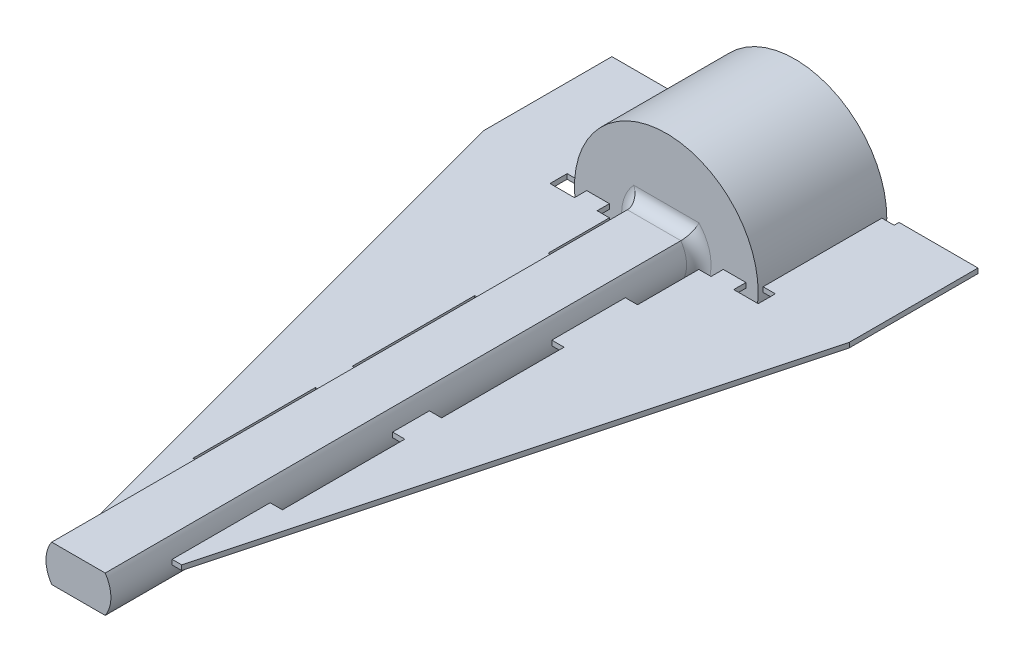
SolidWorks part; units mm, degrees
material "Polylactic Acid (PLA)"
ref_plane "Front Plane" through (0, 0, 0) normal (0, 0, 1) x (1, 0, 0)
ref_plane "Top Plane" through (0, 0, 0) normal (0, 1, 0) x (1, 0, 0)
ref_plane "Right Plane" through (0, 0, 0) normal (1, 0, 0) x (0, 0, -1)
sketch "Sketch2" plane through (0, 0, 0) normal (0, 0, 1) x (1, 0, 0)
  arc A0 (-180.9646, 16.9181) -> (-181.2813, 16.5945) centre (-180.7258, 16.3677) ccw
  arc A1 (-181.2813, 16.5945) -> (-181.4587, 15.6283) centre (-179.0594, 15.6871) ccw
  arc A2 (-181.4587, 15.6283) -> (-180.9368, 15.2683) centre (-178.5779, 19.2465) ccw
  arc A3 (-180.9368, 15.2683) -> (-180.0966, 15.7774) centre (-181.7341, 17.532) ccw
  arc A4 (-180.0966, 15.7774) -> (-179.9066, 16.1884) centre (-180.506, 16.216) ccw
  arc A5 (-179.7695, 16.2766) -> (-179.9066, 16.1884) centre (-179.8067, 16.1838) ccw
  arc A6 (-179.7695, 16.2766) -> (-179.5312, 16.1918) centre (-178.5779, 19.2465) ccw
  arc A7 (-179.4806, 16.0368) -> (-179.5312, 16.1918) centre (-179.561, 16.0963) ccw
  arc A8 (-179.4806, 16.0368) -> (-179.5931, 15.5981) centre (-178.9987, 15.6794) ccw
  arc A9 (-179.5931, 15.5981) -> (-179.2637, 14.6726) centre (-177.2152, 15.9232) ccw
  arc A10 (-179.2637, 14.6726) -> (-178.6317, 14.6218) centre (-178.5779, 19.2465) ccw
  arc A11 (-178.6317, 14.6218) -> (-178.1586, 15.4828) centre (-180.454, 16.1836) ccw
  arc A12 (-178.1586, 15.4828) -> (-178.1996, 15.9338) centre (-178.7324, 15.658) ccw
  arc A13 (-178.1249, 16.0787) -> (-178.1996, 15.9338) centre (-178.1108, 15.9797) ccw
  arc A14 (-178.1249, 16.0787) -> (-177.8761, 16.1244) centre (-178.5779, 19.2465) ccw
  arc A15 (-177.7548, 16.0154) -> (-177.8761, 16.1244) centre (-177.8542, 16.0268) ccw
  arc A16 (-177.7548, 16.0154) -> (-177.6329, 15.5793) centre (-177.1587, 15.9469) ccw
  arc A17 (-177.6329, 15.5793) -> (-176.8848, 14.9425) centre (-175.7362, 17.0498) ccw
  arc A18 (-176.8848, 14.9425) -> (-176.3121, 15.2145) centre (-178.5779, 19.2465) ccw
  arc A19 (-176.3121, 15.2145) -> (-176.3329, 16.1967) centre (-178.6712, 15.6559) ccw
  arc A20 (-176.3329, 16.1967) -> (-176.5939, 16.5668) centre (-176.9175, 16.0615) ccw
  arc A21 (-176.6017, 16.7296) -> (-176.5939, 16.5668) centre (-176.54, 16.651) ccw
  arc A22 (-176.6017, 16.7296) -> (-176.4091, 16.8936) centre (-178.5779, 19.2465) ccw
  arc A23 (-176.2496, 16.8599) -> (-176.4091, 16.8936) centre (-176.3413, 16.8201) ccw
  arc A24 (-176.2496, 16.8599) -> (-175.926, 16.5431) centre (-175.6991, 17.0986) ccw
  arc A25 (-175.926, 16.5431) -> (-174.9597, 16.3657) centre (-175.0185, 18.765) ccw
  arc A26 (-174.9597, 16.3657) -> (-174.5997, 16.8876) centre (-178.5779, 19.2465) ccw
  arc A27 (-174.5997, 16.8876) -> (-175.1088, 17.7278) centre (-176.8634, 16.0903) ccw
  arc A28 (-175.1088, 17.7278) -> (-175.5198, 17.9178) centre (-175.5475, 17.3184) ccw
  arc A29 (-175.608, 18.0549) -> (-175.5198, 17.9178) centre (-175.5152, 18.0177) ccw
  arc A30 (-175.608, 18.0549) -> (-175.5232, 18.2932) centre (-178.5779, 19.2465) ccw
  arc A31 (-175.3682, 18.3438) -> (-175.5232, 18.2932) centre (-175.4277, 18.2635) ccw
  arc A32 (-175.3682, 18.3438) -> (-174.9296, 18.2313) centre (-175.0108, 18.8258) ccw
  arc A33 (-174.9296, 18.2313) -> (-174.004, 18.5608) centre (-175.2546, 20.6092) ccw
  arc A34 (-174.004, 18.5608) -> (-173.9532, 19.1927) centre (-178.5779, 19.2465) ccw
  arc A35 (-173.9532, 19.1927) -> (-174.8142, 19.6658) centre (-175.515, 17.3704) ccw
  arc A36 (-174.8142, 19.6658) -> (-175.2652, 19.6248) centre (-174.9894, 19.092) ccw
  arc A37 (-175.4102, 19.6995) -> (-175.2652, 19.6248) centre (-175.3112, 19.7137) ccw
  arc A38 (-175.4102, 19.6995) -> (-175.4558, 19.9483) centre (-178.5779, 19.2465) ccw
  arc A39 (-175.3469, 20.0696) -> (-175.4558, 19.9483) centre (-175.3583, 19.9702) ccw
  arc A40 (-175.3469, 20.0696) -> (-174.9108, 20.1915) centre (-175.2784, 20.6657) ccw
  arc A41 (-174.9108, 20.1915) -> (-174.274, 20.9396) centre (-176.3812, 22.0882) ccw
  arc A42 (-174.274, 20.9396) -> (-174.5459, 21.5123) centre (-178.5779, 19.2465) ccw
  arc A43 (-174.5459, 21.5123) -> (-175.5282, 21.4915) centre (-174.9873, 19.1532) ccw
  arc A44 (-175.5282, 21.4915) -> (-175.8982, 21.2305) centre (-175.3929, 20.9069) ccw
  arc A45 (-176.0611, 21.2227) -> (-175.8982, 21.2305) centre (-175.9824, 21.2845) ccw
  arc A46 (-176.0611, 21.2227) -> (-176.225, 21.4153) centre (-178.5779, 19.2465) ccw
  arc A47 (-176.1913, 21.5749) -> (-176.225, 21.4153) centre (-176.1515, 21.4831) ccw
  arc A48 (-176.1913, 21.5749) -> (-175.8746, 21.8985) centre (-176.43, 22.1253) ccw
  arc A49 (-175.8746, 21.8985) -> (-175.6971, 22.8647) centre (-178.0964, 22.8059) ccw
  arc A50 (-175.6971, 22.8647) -> (-176.219, 23.2247) centre (-178.5779, 19.2465) ccw
  arc A51 (-176.219, 23.2247) -> (-177.0592, 22.7156) centre (-175.4217, 20.961) ccw
  arc A52 (-177.0592, 22.7156) -> (-177.2492, 22.3046) centre (-176.6499, 22.277) ccw
  arc A53 (-177.3864, 22.2164) -> (-177.2492, 22.3046) centre (-177.3491, 22.3092) ccw
  arc A54 (-177.3864, 22.2164) -> (-177.6247, 22.3012) centre (-178.5779, 19.2465) ccw
  arc A55 (-177.6752, 22.4562) -> (-177.6247, 22.3012) centre (-177.5949, 22.3967) ccw
  arc A56 (-177.6752, 22.4562) -> (-177.5627, 22.8948) centre (-178.1572, 22.8136) ccw
  arc A57 (-177.5627, 22.8948) -> (-177.8922, 23.8204) centre (-179.9406, 22.5698) ccw
  arc A58 (-177.8922, 23.8204) -> (-178.5242, 23.8712) centre (-178.5779, 19.2465) ccw
  arc A59 (-178.5242, 23.8712) -> (-178.9973, 23.0102) centre (-176.7018, 22.3094) ccw
  arc A60 (-178.9973, 23.0102) -> (-178.9563, 22.5592) centre (-178.4234, 22.835) ccw
  arc A61 (-179.0309, 22.4143) -> (-178.9563, 22.5592) centre (-179.0451, 22.5133) ccw
  arc A62 (-179.0309, 22.4143) -> (-179.2797, 22.3686) centre (-178.5779, 19.2465) ccw
  arc A63 (-179.401, 22.4776) -> (-179.2797, 22.3686) centre (-179.3017, 22.4661) ccw
  arc A64 (-179.401, 22.4776) -> (-179.5229, 22.9137) centre (-179.9971, 22.546) ccw
  arc A65 (-179.5229, 22.9137) -> (-180.271, 23.5505) centre (-181.4197, 21.4432) ccw
  arc A66 (-180.271, 23.5505) -> (-180.8437, 23.2785) centre (-178.5779, 19.2465) ccw
  arc A67 (-180.8437, 23.2785) -> (-180.8229, 22.2963) centre (-178.4846, 22.8371) ccw
  arc A68 (-180.8229, 22.2963) -> (-180.562, 21.9262) centre (-180.2383, 22.4315) ccw
  arc A69 (-180.5541, 21.7634) -> (-180.562, 21.9262) centre (-180.6159, 21.842) ccw
  arc A70 (-180.5541, 21.7634) -> (-180.7468, 21.5994) centre (-178.5779, 19.2465) ccw
  arc A71 (-180.9063, 21.6331) -> (-180.7468, 21.5994) centre (-180.8145, 21.6729) ccw
  arc A72 (-180.9063, 21.6331) -> (-181.2299, 21.9499) centre (-181.4567, 21.3944) ccw
  arc A73 (-181.2299, 21.9499) -> (-182.1962, 22.1273) centre (-182.1373, 19.728) ccw
  arc A74 (-182.1962, 22.1273) -> (-182.5561, 21.6054) centre (-178.5779, 19.2465) ccw
  arc A75 (-182.5561, 21.6054) -> (-182.047, 20.7652) centre (-180.2924, 22.4027) ccw
  arc A76 (-182.047, 20.7652) -> (-181.636, 20.5752) centre (-181.6084, 21.1746) ccw
  arc A77 (-181.5478, 20.4381) -> (-181.636, 20.5752) centre (-181.6406, 20.4753) ccw
  arc A78 (-181.5478, 20.4381) -> (-181.6326, 20.1997) centre (-178.5779, 19.2465) ccw
  arc A79 (-181.7877, 20.1492) -> (-181.6326, 20.1997) centre (-181.7281, 20.2295) ccw
  arc A80 (-181.7877, 20.1492) -> (-182.2263, 20.2617) centre (-182.145, 19.6672) ccw
  arc A81 (-182.2263, 20.2617) -> (-183.1518, 19.9322) centre (-181.9012, 17.8838) ccw
  arc A82 (-183.1518, 19.9322) -> (-183.2026, 19.3002) centre (-178.5779, 19.2465) ccw
  arc A83 (-183.2026, 19.3002) -> (-182.3416, 18.8272) centre (-181.6408, 21.1226) ccw
  arc A84 (-182.3416, 18.8272) -> (-181.8906, 18.8681) centre (-182.1664, 19.401) ccw
  arc A85 (-181.7457, 18.7935) -> (-181.8906, 18.8681) centre (-181.8447, 18.7793) ccw
  arc A86 (-181.7457, 18.7935) -> (-181.7, 18.5447) centre (-178.5779, 19.2465) ccw
  arc A87 (-181.809, 18.4234) -> (-181.7, 18.5447) centre (-181.7976, 18.5227) ccw
  arc A88 (-181.809, 18.4234) -> (-182.2451, 18.3015) centre (-181.8775, 17.8273) ccw
  arc A89 (-182.2451, 18.3015) -> (-182.8819, 17.5534) centre (-180.7746, 16.4047) ccw
  arc A90 (-182.8819, 17.5534) -> (-182.6099, 16.9807) centre (-178.5779, 19.2465) ccw
  arc A91 (-182.6099, 16.9807) -> (-181.6277, 17.0015) centre (-182.1685, 19.3398) ccw
  arc A92 (-181.6277, 17.0015) -> (-181.2576, 17.2625) centre (-181.7629, 17.5861) ccw
  arc A93 (-181.0948, 17.2703) -> (-181.2576, 17.2625) centre (-181.1734, 17.2085) ccw
  arc A94 (-181.0948, 17.2703) -> (-180.9308, 17.0777) centre (-178.5779, 19.2465) ccw
  arc A95 (-180.9646, 16.9181) -> (-180.9308, 17.0777) centre (-181.0043, 17.0099) ccw
  arc A96 (-180.9248, 16.8264) -> (-181.1887, 16.5567) centre (-180.7258, 16.3677) ccw
  arc A97 (-181.1887, 16.5567) -> (-181.3594, 15.6773) centre (-179.0594, 15.6871) ccw
  arc A98 (-181.3594, 15.6773) -> (-180.9262, 15.3785) centre (-178.5779, 19.2465) ccw
  arc A99 (-180.9262, 15.3785) -> (-180.1648, 15.8505) centre (-181.7341, 17.532) ccw
  arc A100 (-180.1648, 15.8505) -> (-180.0065, 16.193) centre (-180.506, 16.216) ccw
  arc A101 (-179.7323, 16.3694) -> (-180.0065, 16.193) centre (-179.8067, 16.1838) ccw
  arc A102 (-179.7323, 16.3694) -> (-179.5014, 16.2872) centre (-178.5779, 19.2465) ccw
  arc A103 (-179.4003, 15.9772) -> (-179.5014, 16.2872) centre (-179.561, 16.0963) ccw
  arc A104 (-179.4003, 15.9772) -> (-179.494, 15.6117) centre (-178.9987, 15.6794) ccw
  arc A105 (-179.494, 15.6117) -> (-179.2022, 14.7648) centre (-177.2152, 15.9232) ccw
  arc A106 (-179.2022, 14.7648) -> (-178.6776, 14.7226) centre (-178.5779, 19.2465) ccw
  arc A107 (-178.6776, 14.7226) -> (-178.2542, 15.512) centre (-180.454, 16.1836) ccw
  arc A108 (-178.2542, 15.512) -> (-178.2884, 15.8878) centre (-178.7324, 15.658) ccw
  arc A109 (-178.1391, 16.1777) -> (-178.2884, 15.8878) centre (-178.1108, 15.9797) ccw
  arc A110 (-178.1391, 16.1777) -> (-177.898, 16.222) centre (-178.5779, 19.2465) ccw
  arc A111 (-177.6555, 16.004) -> (-177.898, 16.222) centre (-177.8542, 16.0268) ccw
  arc A112 (-177.6555, 16.004) -> (-177.5539, 15.6406) centre (-177.1587, 15.9469) ccw
  arc A113 (-177.5539, 15.6406) -> (-176.8777, 15.0531) centre (-175.7362, 17.0498) ccw
  arc A114 (-176.8777, 15.0531) -> (-176.4023, 15.2788) centre (-178.5779, 19.2465) ccw
  arc A115 (-176.4023, 15.2788) -> (-176.4304, 16.1742) centre (-178.6712, 15.6559) ccw
  arc A116 (-176.4304, 16.1742) -> (-176.6478, 16.4826) centre (-176.9175, 16.0615) ccw
  arc A117 (-176.6635, 16.8083) -> (-176.6478, 16.4826) centre (-176.54, 16.651) ccw
  arc A118 (-176.6635, 16.8083) -> (-176.4769, 16.9671) centre (-178.5779, 19.2465) ccw
  arc A119 (-176.1578, 16.8996) -> (-176.4769, 16.9671) centre (-176.3413, 16.8201) ccw
  arc A120 (-176.1578, 16.8996) -> (-175.8881, 16.6357) centre (-175.6991, 17.0986) ccw
  arc A121 (-175.8881, 16.6357) -> (-175.0088, 16.465) centre (-175.0185, 18.765) ccw
  arc A122 (-175.0088, 16.465) -> (-174.71, 16.8982) centre (-178.5779, 19.2465) ccw
  arc A123 (-174.71, 16.8982) -> (-175.1819, 17.6596) centre (-176.8634, 16.0903) ccw
  arc A124 (-175.1819, 17.6596) -> (-175.5244, 17.8179) centre (-175.5475, 17.3184) ccw
  arc A125 (-175.7009, 18.0922) -> (-175.5244, 17.8179) centre (-175.5152, 18.0177) ccw
  arc A126 (-175.7009, 18.0922) -> (-175.6187, 18.323) centre (-178.5779, 19.2465) ccw
  arc A127 (-175.3086, 18.4241) -> (-175.6187, 18.323) centre (-175.4277, 18.2635) ccw
  arc A128 (-175.3086, 18.4241) -> (-174.9431, 18.3304) centre (-175.0108, 18.8258) ccw
  arc A129 (-174.9431, 18.3304) -> (-174.0962, 18.6222) centre (-175.2546, 20.6092) ccw
  arc A130 (-174.0962, 18.6222) -> (-174.054, 19.1468) centre (-178.5779, 19.2465) ccw
  arc A131 (-174.054, 19.1468) -> (-174.8434, 19.5702) centre (-175.515, 17.3704) ccw
  arc A132 (-174.8434, 19.5702) -> (-175.2192, 19.536) centre (-174.9894, 19.092) ccw
  arc A133 (-175.5091, 19.6853) -> (-175.2192, 19.536) centre (-175.3112, 19.7137) ccw
  arc A134 (-175.5091, 19.6853) -> (-175.5534, 19.9264) centre (-178.5779, 19.2465) ccw
  arc A135 (-175.3354, 20.1689) -> (-175.5534, 19.9264) centre (-175.3583, 19.9702) ccw
  arc A136 (-175.3354, 20.1689) -> (-174.972, 20.2705) centre (-175.2784, 20.6657) ccw
  arc A137 (-174.972, 20.2705) -> (-174.3845, 20.9467) centre (-176.3812, 22.0882) ccw
  arc A138 (-174.3845, 20.9467) -> (-174.6103, 21.4221) centre (-178.5779, 19.2465) ccw
  arc A139 (-174.6103, 21.4221) -> (-175.5056, 21.3941) centre (-174.9873, 19.1532) ccw
  arc A140 (-175.5056, 21.3941) -> (-175.814, 21.1766) centre (-175.3929, 20.9069) ccw
  arc A141 (-176.1397, 21.1609) -> (-175.814, 21.1766) centre (-175.9824, 21.2845) ccw
  arc A142 (-176.1397, 21.1609) -> (-176.2986, 21.3476) centre (-178.5779, 19.2465) ccw
  arc A143 (-176.2311, 21.6666) -> (-176.2986, 21.3476) centre (-176.1515, 21.4831) ccw
  arc A144 (-176.2311, 21.6666) -> (-175.9671, 21.9363) centre (-176.43, 22.1253) ccw
  arc A145 (-175.9671, 21.9363) -> (-175.7964, 22.8156) centre (-178.0964, 22.8059) ccw
  arc A146 (-175.7964, 22.8156) -> (-176.2296, 23.1145) centre (-178.5779, 19.2465) ccw
  arc A147 (-176.2296, 23.1145) -> (-176.991, 22.6425) centre (-175.4217, 20.961) ccw
  arc A148 (-176.991, 22.6425) -> (-177.1493, 22.3) centre (-176.6499, 22.277) ccw
  arc A149 (-177.4236, 22.1236) -> (-177.1493, 22.3) centre (-177.3491, 22.3092) ccw
  arc A150 (-177.4236, 22.1236) -> (-177.6545, 22.2058) centre (-178.5779, 19.2465) ccw
  arc A151 (-177.7555, 22.5158) -> (-177.6545, 22.2058) centre (-177.5949, 22.3967) ccw
  arc A152 (-177.7555, 22.5158) -> (-177.6618, 22.8813) centre (-178.1572, 22.8136) ccw
  arc A153 (-177.6618, 22.8813) -> (-177.9536, 23.7282) centre (-179.9406, 22.5698) ccw
  arc A154 (-177.9536, 23.7282) -> (-178.4782, 23.7704) centre (-178.5779, 19.2465) ccw
  arc A155 (-178.4782, 23.7704) -> (-178.9016, 22.981) centre (-176.7018, 22.3094) ccw
  arc A156 (-178.9016, 22.981) -> (-178.8675, 22.6052) centre (-178.4234, 22.835) ccw
  arc A157 (-179.0168, 22.3153) -> (-178.8675, 22.6052) centre (-179.0451, 22.5133) ccw
  arc A158 (-179.0168, 22.3153) -> (-179.2578, 22.271) centre (-178.5779, 19.2465) ccw
  arc A159 (-179.5004, 22.489) -> (-179.2578, 22.271) centre (-179.3017, 22.4661) ccw
  arc A160 (-179.5004, 22.489) -> (-179.6019, 22.8524) centre (-179.9971, 22.546) ccw
  arc A161 (-179.6019, 22.8524) -> (-180.2781, 23.4399) centre (-181.4197, 21.4432) ccw
  arc A162 (-180.2781, 23.4399) -> (-180.7535, 23.2142) centre (-178.5779, 19.2465) ccw
  arc A163 (-180.7535, 23.2142) -> (-180.7255, 22.3188) centre (-178.4846, 22.8371) ccw
  arc A164 (-180.7255, 22.3188) -> (-180.508, 22.0104) centre (-180.2383, 22.4315) ccw
  arc A165 (-180.4924, 21.6847) -> (-180.508, 22.0104) centre (-180.6159, 21.842) ccw
  arc A166 (-180.4924, 21.6847) -> (-180.679, 21.5259) centre (-178.5779, 19.2465) ccw
  arc A167 (-180.998, 21.5933) -> (-180.679, 21.5259) centre (-180.8145, 21.6729) ccw
  arc A168 (-180.998, 21.5933) -> (-181.2677, 21.8573) centre (-181.4567, 21.3944) ccw
  arc A169 (-181.2677, 21.8573) -> (-182.1471, 22.028) centre (-182.1373, 19.728) ccw
  arc A170 (-182.1471, 22.028) -> (-182.4459, 21.5948) centre (-178.5779, 19.2465) ccw
  arc A171 (-182.4459, 21.5948) -> (-181.9739, 20.8334) centre (-180.2924, 22.4027) ccw
  arc A172 (-181.9739, 20.8334) -> (-181.6314, 20.6751) centre (-181.6084, 21.1746) ccw
  arc A173 (-181.455, 20.4008) -> (-181.6314, 20.6751) centre (-181.6406, 20.4753) ccw
  arc A174 (-181.455, 20.4008) -> (-181.5372, 20.17) centre (-178.5779, 19.2465) ccw
  arc A175 (-181.8472, 20.0689) -> (-181.5372, 20.17) centre (-181.7281, 20.2295) ccw
  arc A176 (-181.8472, 20.0689) -> (-182.2127, 20.1626) centre (-182.145, 19.6672) ccw
  arc A177 (-182.2127, 20.1626) -> (-183.0597, 19.8708) centre (-181.9012, 17.8838) ccw
  arc A178 (-183.0597, 19.8708) -> (-183.1018, 19.3462) centre (-178.5779, 19.2465) ccw
  arc A179 (-183.1018, 19.3462) -> (-182.3124, 18.9228) centre (-181.6408, 21.1226) ccw
  arc A180 (-182.3124, 18.9228) -> (-181.9366, 18.9569) centre (-182.1664, 19.401) ccw
  arc A181 (-181.6467, 18.8076) -> (-181.9366, 18.9569) centre (-181.8447, 18.7793) ccw
  arc A182 (-181.6467, 18.8076) -> (-181.6024, 18.5666) centre (-178.5779, 19.2465) ccw
  arc A183 (-181.8204, 18.324) -> (-181.6024, 18.5666) centre (-181.7976, 18.5227) ccw
  arc A184 (-181.8204, 18.324) -> (-182.1838, 18.2225) centre (-181.8775, 17.8273) ccw
  arc A185 (-182.1838, 18.2225) -> (-182.7714, 17.5463) centre (-180.7746, 16.4047) ccw
  arc A186 (-182.7714, 17.5463) -> (-182.5456, 17.0709) centre (-178.5779, 19.2465) ccw
  arc A187 (-182.5456, 17.0709) -> (-181.6502, 17.0989) centre (-182.1685, 19.3398) ccw
  arc A188 (-181.6502, 17.0989) -> (-181.3419, 17.3164) centre (-181.7629, 17.5861) ccw
  arc A189 (-181.0161, 17.332) -> (-181.3419, 17.3164) centre (-181.1734, 17.2085) ccw
  arc A190 (-181.0161, 17.332) -> (-180.8573, 17.1454) centre (-178.5779, 19.2465) ccw
  arc A191 (-180.9248, 16.8264) -> (-180.8573, 17.1454) centre (-181.0043, 17.0099) ccw
  arc A192 (-180.9248, 16.8264) -> (-181.1887, 16.5567) centre (-180.7258, 16.3677) ccw construction
  arc A193 (-181.1887, 16.5567) -> (-181.3594, 15.6773) centre (-179.0594, 15.6871) ccw construction
  arc A194 (-181.3594, 15.6773) -> (-180.9262, 15.3785) centre (-178.5779, 19.2465) ccw construction
  arc A195 (-180.9262, 15.3785) -> (-180.1648, 15.8505) centre (-181.7341, 17.532) ccw construction
  arc A196 (-180.1648, 15.8505) -> (-180.0065, 16.193) centre (-180.506, 16.216) ccw construction
  arc A197 (-179.7323, 16.3694) -> (-180.0065, 16.193) centre (-179.8067, 16.1838) ccw construction
  arc A198 (-179.7323, 16.3694) -> (-179.5014, 16.2872) centre (-178.5779, 19.2465) ccw construction
  arc A199 (-179.4003, 15.9772) -> (-179.5014, 16.2872) centre (-179.561, 16.0963) ccw construction
  arc A200 (-179.4003, 15.9772) -> (-179.494, 15.6117) centre (-178.9987, 15.6794) ccw construction
  arc A201 (-179.494, 15.6117) -> (-179.2022, 14.7648) centre (-177.2152, 15.9232) ccw construction
  arc A202 (-179.2022, 14.7648) -> (-178.6776, 14.7226) centre (-178.5779, 19.2465) ccw construction
  arc A203 (-178.6776, 14.7226) -> (-178.2542, 15.512) centre (-180.454, 16.1836) ccw construction
  arc A204 (-178.2542, 15.512) -> (-178.2884, 15.8878) centre (-178.7324, 15.658) ccw construction
  arc A205 (-178.1391, 16.1777) -> (-178.2884, 15.8878) centre (-178.1108, 15.9797) ccw construction
  arc A206 (-178.1391, 16.1777) -> (-177.898, 16.222) centre (-178.5779, 19.2465) ccw construction
  arc A207 (-177.6555, 16.004) -> (-177.898, 16.222) centre (-177.8542, 16.0268) ccw construction
  arc A208 (-177.6555, 16.004) -> (-177.5539, 15.6406) centre (-177.1587, 15.9469) ccw construction
  arc A209 (-177.5539, 15.6406) -> (-176.8777, 15.0531) centre (-175.7362, 17.0498) ccw construction
  arc A210 (-176.8777, 15.0531) -> (-176.4023, 15.2788) centre (-178.5779, 19.2465) ccw construction
  arc A211 (-176.4023, 15.2788) -> (-176.4304, 16.1742) centre (-178.6712, 15.6559) ccw construction
  arc A212 (-176.4304, 16.1742) -> (-176.6478, 16.4826) centre (-176.9175, 16.0615) ccw construction
  arc A213 (-176.6635, 16.8083) -> (-176.6478, 16.4826) centre (-176.54, 16.651) ccw construction
  arc A214 (-176.6635, 16.8083) -> (-176.4769, 16.9671) centre (-178.5779, 19.2465) ccw construction
  arc A215 (-176.1578, 16.8996) -> (-176.4769, 16.9671) centre (-176.3413, 16.8201) ccw construction
  arc A216 (-176.1578, 16.8996) -> (-175.8881, 16.6357) centre (-175.6991, 17.0986) ccw construction
  arc A217 (-175.8881, 16.6357) -> (-175.0088, 16.465) centre (-175.0185, 18.765) ccw construction
  arc A218 (-175.0088, 16.465) -> (-174.71, 16.8982) centre (-178.5779, 19.2465) ccw construction
  arc A219 (-174.71, 16.8982) -> (-175.1819, 17.6596) centre (-176.8634, 16.0903) ccw construction
  arc A220 (-175.1819, 17.6596) -> (-175.5244, 17.8179) centre (-175.5475, 17.3184) ccw construction
  arc A221 (-175.7009, 18.0922) -> (-175.5244, 17.8179) centre (-175.5152, 18.0177) ccw construction
  arc A222 (-175.7009, 18.0922) -> (-175.6187, 18.323) centre (-178.5779, 19.2465) ccw construction
  arc A223 (-175.3086, 18.4241) -> (-175.6187, 18.323) centre (-175.4277, 18.2635) ccw construction
  arc A224 (-175.3086, 18.4241) -> (-174.9431, 18.3304) centre (-175.0108, 18.8258) ccw construction
  arc A225 (-174.9431, 18.3304) -> (-174.0962, 18.6222) centre (-175.2546, 20.6092) ccw construction
  arc A226 (-174.0962, 18.6222) -> (-174.054, 19.1468) centre (-178.5779, 19.2465) ccw construction
  arc A227 (-174.054, 19.1468) -> (-174.8434, 19.5702) centre (-175.515, 17.3704) ccw construction
  arc A228 (-174.8434, 19.5702) -> (-175.2192, 19.536) centre (-174.9894, 19.092) ccw construction
  arc A229 (-175.5091, 19.6853) -> (-175.2192, 19.536) centre (-175.3112, 19.7137) ccw construction
  arc A230 (-175.5091, 19.6853) -> (-175.5534, 19.9264) centre (-178.5779, 19.2465) ccw construction
  arc A231 (-175.3354, 20.1689) -> (-175.5534, 19.9264) centre (-175.3583, 19.9702) ccw construction
  arc A232 (-175.3354, 20.1689) -> (-174.972, 20.2705) centre (-175.2784, 20.6657) ccw construction
  arc A233 (-174.972, 20.2705) -> (-174.3845, 20.9467) centre (-176.3812, 22.0882) ccw construction
  arc A234 (-174.3845, 20.9467) -> (-174.6103, 21.4221) centre (-178.5779, 19.2465) ccw construction
  arc A235 (-174.6103, 21.4221) -> (-175.5056, 21.3941) centre (-174.9873, 19.1532) ccw construction
  arc A236 (-175.5056, 21.3941) -> (-175.814, 21.1766) centre (-175.3929, 20.9069) ccw construction
  arc A237 (-176.1397, 21.1609) -> (-175.814, 21.1766) centre (-175.9824, 21.2845) ccw construction
  arc A238 (-176.1397, 21.1609) -> (-176.2986, 21.3476) centre (-178.5779, 19.2465) ccw construction
  arc A239 (-176.2311, 21.6666) -> (-176.2986, 21.3476) centre (-176.1515, 21.4831) ccw construction
  arc A240 (-176.2311, 21.6666) -> (-175.9671, 21.9363) centre (-176.43, 22.1253) ccw construction
  arc A241 (-175.9671, 21.9363) -> (-175.7964, 22.8156) centre (-178.0964, 22.8059) ccw construction
  arc A242 (-175.7964, 22.8156) -> (-176.2296, 23.1145) centre (-178.5779, 19.2465) ccw construction
  arc A243 (-176.2296, 23.1145) -> (-176.991, 22.6425) centre (-175.4217, 20.961) ccw construction
  arc A244 (-176.991, 22.6425) -> (-177.1493, 22.3) centre (-176.6499, 22.277) ccw construction
  arc A245 (-177.4236, 22.1236) -> (-177.1493, 22.3) centre (-177.3491, 22.3092) ccw construction
  arc A246 (-177.4236, 22.1236) -> (-177.6545, 22.2058) centre (-178.5779, 19.2465) ccw construction
  arc A247 (-177.7555, 22.5158) -> (-177.6545, 22.2058) centre (-177.5949, 22.3967) ccw construction
  arc A248 (-177.7555, 22.5158) -> (-177.6618, 22.8813) centre (-178.1572, 22.8136) ccw construction
  arc A249 (-177.6618, 22.8813) -> (-177.9536, 23.7282) centre (-179.9406, 22.5698) ccw construction
  arc A250 (-177.9536, 23.7282) -> (-178.4782, 23.7704) centre (-178.5779, 19.2465) ccw construction
  arc A251 (-178.4782, 23.7704) -> (-178.9016, 22.981) centre (-176.7018, 22.3094) ccw construction
  arc A252 (-178.9016, 22.981) -> (-178.8675, 22.6052) centre (-178.4234, 22.835) ccw construction
  arc A253 (-179.0168, 22.3153) -> (-178.8675, 22.6052) centre (-179.0451, 22.5133) ccw construction
  arc A254 (-179.0168, 22.3153) -> (-179.2578, 22.271) centre (-178.5779, 19.2465) ccw construction
  arc A255 (-179.5004, 22.489) -> (-179.2578, 22.271) centre (-179.3017, 22.4661) ccw construction
  arc A256 (-179.5004, 22.489) -> (-179.6019, 22.8524) centre (-179.9971, 22.546) ccw construction
  arc A257 (-179.6019, 22.8524) -> (-180.2781, 23.4399) centre (-181.4197, 21.4432) ccw construction
  arc A258 (-180.2781, 23.4399) -> (-180.7535, 23.2142) centre (-178.5779, 19.2465) ccw construction
  arc A259 (-180.7535, 23.2142) -> (-180.7255, 22.3188) centre (-178.4846, 22.8371) ccw construction
  arc A260 (-180.7255, 22.3188) -> (-180.508, 22.0104) centre (-180.2383, 22.4315) ccw construction
  arc A261 (-180.4924, 21.6847) -> (-180.508, 22.0104) centre (-180.6159, 21.842) ccw construction
  arc A262 (-180.4924, 21.6847) -> (-180.679, 21.5259) centre (-178.5779, 19.2465) ccw construction
  arc A263 (-180.998, 21.5933) -> (-180.679, 21.5259) centre (-180.8145, 21.6729) ccw construction
  arc A264 (-180.998, 21.5933) -> (-181.2677, 21.8573) centre (-181.4567, 21.3944) ccw construction
  arc A265 (-181.2677, 21.8573) -> (-182.1471, 22.028) centre (-182.1373, 19.728) ccw construction
  arc A266 (-182.1471, 22.028) -> (-182.4459, 21.5948) centre (-178.5779, 19.2465) ccw construction
  arc A267 (-182.4459, 21.5948) -> (-181.9739, 20.8334) centre (-180.2924, 22.4027) ccw construction
  arc A268 (-181.9739, 20.8334) -> (-181.6314, 20.6751) centre (-181.6084, 21.1746) ccw construction
  arc A269 (-181.455, 20.4008) -> (-181.6314, 20.6751) centre (-181.6406, 20.4753) ccw construction
  arc A270 (-181.455, 20.4008) -> (-181.5372, 20.17) centre (-178.5779, 19.2465) ccw construction
  arc A271 (-181.8472, 20.0689) -> (-181.5372, 20.17) centre (-181.7281, 20.2295) ccw construction
  arc A272 (-181.8472, 20.0689) -> (-182.2127, 20.1626) centre (-182.145, 19.6672) ccw construction
  arc A273 (-182.2127, 20.1626) -> (-183.0597, 19.8708) centre (-181.9012, 17.8838) ccw construction
  arc A274 (-183.0597, 19.8708) -> (-183.1018, 19.3462) centre (-178.5779, 19.2465) ccw construction
  arc A275 (-183.1018, 19.3462) -> (-182.3124, 18.9228) centre (-181.6408, 21.1226) ccw construction
  arc A276 (-182.3124, 18.9228) -> (-181.9366, 18.9569) centre (-182.1664, 19.401) ccw construction
  arc A277 (-181.6467, 18.8076) -> (-181.9366, 18.9569) centre (-181.8447, 18.7793) ccw construction
  arc A278 (-181.6467, 18.8076) -> (-181.6024, 18.5666) centre (-178.5779, 19.2465) ccw construction
  arc A279 (-181.8204, 18.324) -> (-181.6024, 18.5666) centre (-181.7976, 18.5227) ccw construction
  arc A280 (-181.8204, 18.324) -> (-182.1838, 18.2225) centre (-181.8775, 17.8273) ccw construction
  arc A281 (-182.1838, 18.2225) -> (-182.7714, 17.5463) centre (-180.7746, 16.4047) ccw construction
  arc A282 (-182.7714, 17.5463) -> (-182.5456, 17.0709) centre (-178.5779, 19.2465) ccw construction
  arc A283 (-182.5456, 17.0709) -> (-181.6502, 17.0989) centre (-182.1685, 19.3398) ccw construction
  arc A284 (-181.6502, 17.0989) -> (-181.3419, 17.3164) centre (-181.7629, 17.5861) ccw construction
  arc A285 (-181.0161, 17.332) -> (-181.3419, 17.3164) centre (-181.1734, 17.2085) ccw construction
  arc A286 (-181.0161, 17.332) -> (-180.8573, 17.1454) centre (-178.5779, 19.2465) ccw construction
  arc A287 (-180.9248, 16.8264) -> (-180.8573, 17.1454) centre (-181.0043, 17.0099) ccw construction
  circle A288 centre (-178.5779, 19.2465) radius 7.5
  dimension "D3" = 15
  dimension "D1" = 0
  dimension "D2" = 0.1
extrude "Boss-Extrude1" add sketch "Sketch2" against normal offset from surface 0.5 and the other way offset from surface (4 mm away) 1
sketch "Sketch4" plane through (0, 0, 4) normal (0, 0, 1) x (1, 0, 0)
  circle A1 centre (-178.5779, 19.2465) radius 7.5
  circle A2 centre (-178.5779, 19.2465) radius 7.5
  dimension "D1" = 0
extrude "Boss-Extrude2" add sketch "Sketch4" along normal blind 1
sketch "Sketch6" plane through (0, 0, 5) normal (0, 0, 1) x (1, 0, 0)
  line L1 (-180.7625, 20.7465) -> (-176.3933, 20.7465)
  line L2 (-180.7625, 20.7465) -> (-180.7625, 17.7465) construction
  line L3 (-180.7625, 17.7465) -> (-176.3933, 17.7465)
  line L4 (-176.3933, 20.7465) -> (-176.3933, 17.7465) construction
  line L5 (-180.7625, 20.7465) -> (-176.3933, 17.7465) construction
  line L6 (-180.7625, 17.7465) -> (-176.3933, 20.7465) construction
  arc A0 (-180.7625, 20.7465) -> (-180.7625, 17.7465) centre (-178.5779, 19.2465) ccw
  arc A1 (-176.3933, 17.7465) -> (-176.3933, 20.7465) centre (-178.5779, 19.2465) ccw
  dimension "D1" = 5.3
  dimension "D2" = 1.5
extrude "Boss-Extrude3" add sketch "Sketch6" along normal blind 48
fillet "Fillet1" radius 1 4 edges at (-181.2279, 19.2465, 5) (-178.5779, 17.7465, 5) (-175.9279, 19.2465, 5) (-178.5779, 20.7465, 5)
ref_plane "Plane1" through (0, 19.2465, 0) normal (0, 1, 0) x (1, 0, 0)
sketch "Sketch7" plane through (0, 19.2465, 0) normal (0, 1, 0) x (1, 0, 0)
  line L1 (-182.2279, -6) -> (-182.2279, -11)
  line L2 (-182.0023, -48) -> (-193.5242, -5)
  line L3 (-187.0779, -6) -> (-185.0779, -6)
  line L5 (-171.0779, 5.5) -> (-186.0779, 5.5) construction
  line L6 (-187.0779, 5.5) -> (-193.5242, 5.5)
  line L7 (-187.0779, 5.5) -> (-187.0779, 5.1)
  line L9 (-193.5242, 5.5) -> (-193.5242, -5)
  line L10 (-186.0779, 5.5) -> (-186.0779, -5) construction
  line L11 (-186.0779, -5) -> (-171.0779, -5) construction
  line L12 (-181.2279, -6) -> (-181.2279, -53) construction
  line L13 (-187.0779, -4.6) -> (-187.0779, -6)
  line L14 (-187.0779, 5.1) -> (-186.0779, 5.1)
  line L16 (-187.0779, -4.6) -> (-186.0779, -4.6)
  line L17 (-186.0779, 5.1) -> (-186.0779, -4.6)
  line L19 (-185.0779, -5) -> (-183.2279, -5)
  line L20 (-185.0779, -5) -> (-185.0779, -6)
  line L22 (-183.2279, -5) -> (-183.2279, -6)
  line L23 (-182.2279, -11) -> (-181.2279, -11)
  line L25 (-182.2279, -17) -> (-181.2279, -17)
  line L26 (-181.2279, -11) -> (-181.2279, -17)
  line L27 (-182.2279, -27) -> (-181.2279, -27)
  line L29 (-182.2279, -30) -> (-181.2279, -30)
  line L30 (-181.2279, -27) -> (-181.2279, -30)
  line L31 (-182.2279, -40) -> (-181.2279, -40)
  line L33 (-182.0023, -48) -> (-181.2279, -48)
  line L34 (-181.2279, -40) -> (-181.2279, -48)
  line L39 (-183.2279, -6) -> (-182.2279, -6)
  line L40 (-182.2279, -17) -> (-182.2279, -27)
  line L41 (-182.2279, -30) -> (-182.2279, -40)
  line L43 (-180.7625, -6) -> (-181.2279, -6) construction
  line L44 (-182.2279, -5) -> (-181.2373, -5) construction
  line L45 (-176.3933, -53) -> (-180.7625, -53) construction
  line L46 (-178.5779, 5.5) -> (-178.5779, -53) construction
  line L47 (-175.1535, -48) -> (-175.9279, -48)
  line L48 (-175.9279, -40) -> (-175.9279, -48)
  line L49 (-174.9279, -40) -> (-175.9279, -40)
  line L50 (-174.9279, -30) -> (-174.9279, -40)
  line L51 (-174.9279, -30) -> (-175.9279, -30)
  line L52 (-175.9279, -27) -> (-175.9279, -30)
  line L53 (-174.9279, -27) -> (-175.9279, -27)
  line L54 (-174.9279, -17) -> (-174.9279, -27)
  line L55 (-174.9279, -17) -> (-175.9279, -17)
  line L56 (-175.9279, -11) -> (-175.9279, -17)
  line L57 (-174.9279, -11) -> (-175.9279, -11)
  line L58 (-174.9279, -6) -> (-174.9279, -11)
  line L59 (-173.9279, -6) -> (-174.9279, -6)
  line L60 (-173.9279, -5) -> (-173.9279, -6)
  line L61 (-172.0779, -5) -> (-173.9279, -5)
  line L62 (-172.0779, -5) -> (-172.0779, -6)
  line L63 (-170.0779, -6) -> (-172.0779, -6)
  line L64 (-170.0779, -4.6) -> (-170.0779, -6)
  line L65 (-170.0779, -4.6) -> (-171.0779, -4.6)
  line L66 (-171.0779, 5.1) -> (-171.0779, -4.6)
  line L67 (-170.0779, 5.1) -> (-171.0779, 5.1)
  line L68 (-170.0779, 5.5) -> (-170.0779, 5.1)
  line L69 (-170.0779, 5.5) -> (-163.6317, 5.5)
  line L70 (-163.6317, 5.5) -> (-163.6317, -5)
  line L71 (-175.1535, -48) -> (-163.6317, -5)
  dimension "D1" = 1
  dimension "D2" = 1
  dimension "D3" = 1
  dimension "D4" = 0.4
  dimension "D5" = 0.4
  dimension "D6" = 1
  dimension "D7" = 1
  dimension "D8" = 5
  dimension "D9" = 10
  dimension "D10" = 10
  dimension "D11" = 5
  dimension "D12" = 12
  dimension "D13" = 25
  dimension "D14" = 15
  dimension "D15" = 15
extrude "Boss-Extrude6" add sketch "Sketch7" along normal mid plane 0.4 separate body
